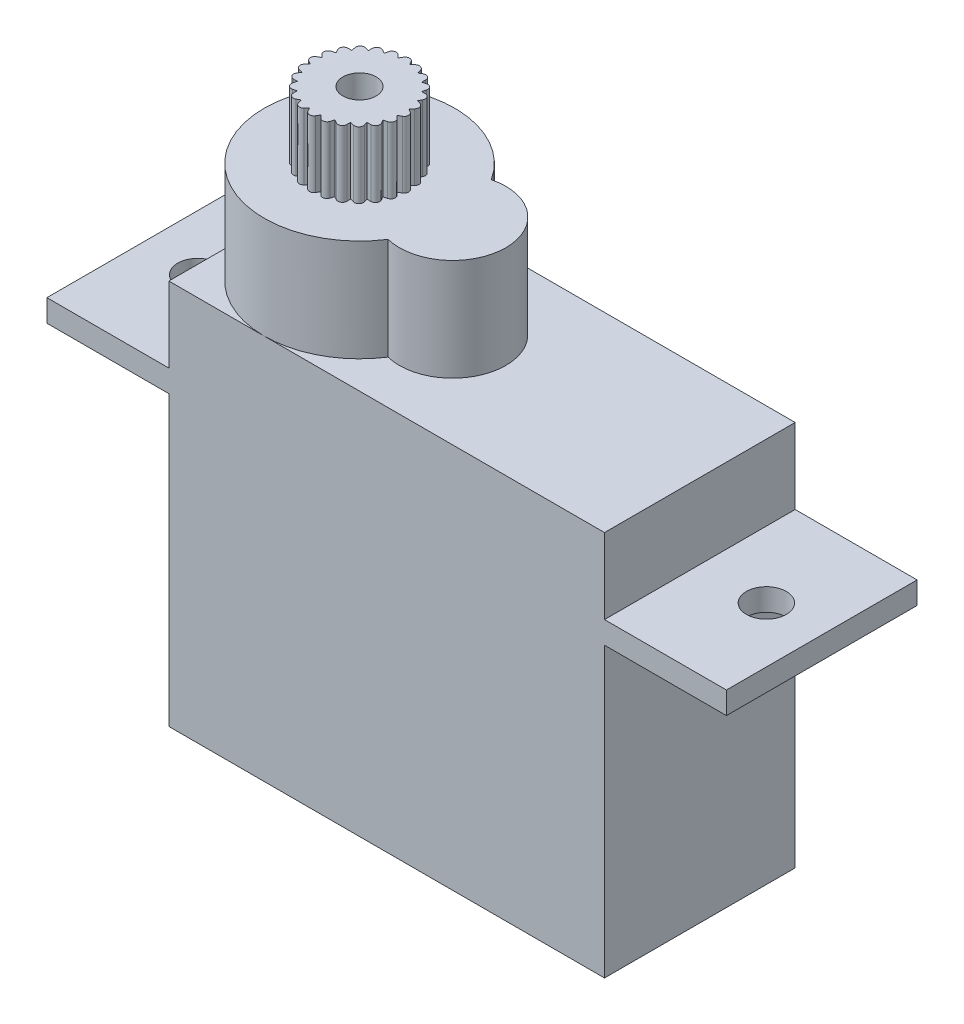
SolidWorks part; units mm, degrees
ref_plane "Plano frontal" through (0, 0, 0) normal (0, 0, 1) x (1, 0, 0)
ref_plane "Plano superior" through (0, 0, 0) normal (0, 1, 0) x (1, 0, 0)
ref_plane "Plano direito" through (0, 0, 0) normal (1, 0, 0) x (0, 0, -1)
sketch "Esboço1" plane through (0, 0, 0) normal (0, 0, 1) x (1, 0, 0)
  line L0 (0, 0) -> (0, 13)
  line L1 (0, 13) -> (-5.5, 13)
  line L2 (-5.5, 13) -> (-5.5, 14)
  line L3 (-5.5, 14) -> (0, 14)
  line L4 (0, 14) -> (0, 17.4)
  line L5 (0, 17.4) -> (19.65, 17.4)
  line L6 (19.65, 17.4) -> (19.65, 14)
  line L7 (19.65, 14) -> (25.15, 14)
  line L8 (25.15, 14) -> (25.15, 13)
  line L9 (25.15, 13) -> (19.65, 13)
  line L10 (19.65, 13) -> (19.65, 0)
  line L11 (19.65, 0) -> (0, 0)
  dimension "D1" = 19.65
  dimension "D2" = 17.4
  dimension "D3" = 30.65
  dimension "D4" = 1
  dimension "D5" = 5.5
  dimension "D7" = 13
  dimension "D6" = 5.5
extrude "Ressalto-extrusão1" add sketch "Esboço1" along normal blind 8.6
sketch "Esboço2" plane through (0, 14, 0) normal (0, 1, 0) x (1, 0, 0)
  line L0 (0, 0) -> (-5.5, 0) construction
  line L1 (-5.5, -8.6) -> (-5.5, 0) construction
  line L2 (25.15, -8.6) -> (25.15, 0) construction
  circle A0 centre (-3, -4.3) radius 0.9
  circle A1 centre (22.65, -4.3) radius 0.9
  dimension "D1" = 1.8
  dimension "D2" = 4.3
  dimension "D3" = 2.5
  dimension "D4" = 2.5
extrude "Corte-extrusão1" cut sketch "Esboço2" against normal through all
sketch "Esboço3" plane through (0, 17.4, 0) normal (0, 1, 0) x (1, 0, 0)
  line L0 (0, -8.6) -> (0, 0) construction
  line L4 (-5.5, -4.3) -> (25.15, -4.3) construction
  line L5 (8.5, -6.7) -> (8.7336, -6.7)
  line L6 (8.5, -6.7) -> (6.1, -6.7)
  line L7 (8.5, -1.9) -> (6.1, -1.9)
  line L8 (6.1, -1.9) -> (6.1, -6.7)
  line L9 (-5.5, -8.6) -> (-5.5, 0) construction
  line L10 (25.15, -8.6) -> (25.15, 0) construction
  circle A0 centre (4.3, -4.3) radius 4.3
  circle A1 centre (8.5, -4.3) radius 2.4
  dimension "D2" = 4.8
  dimension "D1" = 8.6
  dimension "D3" = 8.5
extrude "Ressalto-extrusão3" add sketch "Esboço3" along normal blind 4.6 contours A0 L4 L8 L7 | L4 A0 L6 L8 | A1 A0 L7 L8 | A1 L4 A0 | A0 L4 A1 | L4 A0 A1 | L4 A1 A0 | A1 L8 L6 A0
sketch "Esboço4" plane through (0, 22, 0) normal (0, 1, 0) x (1, 0, 0)
  circle A0 centre (4.3, -4.3) radius 1.9
  arc A1 (7.9155, -1.9723) -> (7.9155, -6.6277) centre (4.3, -4.3) ccw construction
  circle A2 centre (4.3, -4.3) radius 0.75
  dimension "D1" = 3.8
  dimension "D2" = 1.5
extrude "Ressalto-extrusão4" add sketch "Esboço4" along normal blind 3
sketch "Esboço5" plane through (0, 25, 0) normal (0, 1, 0) x (1, 0, 0)
  line L0 (3.9961, -2.4245) -> (4.1471, -2.1647)
  line L1 (4.4935, -2.1657) -> (4.6461, -2.4318)
  line L2 (3.9961, -2.4245) -> (4.6461, -2.4318)
  circle A0 centre (4.3, -4.3) radius 1.9 construction
  circle A1 centre (4.3, -4.3) radius 1.9 construction
  arc A2 (4.1471, -2.1647) -> (4.4935, -2.1657) centre (4.32, -2.2652) cw
  point P6 (4.3211, -2.4281)
  point P10 (4.3211, -1.8652)
  dimension "D3" = 0.2
  dimension "D1" = 0.65
  dimension "D2" = 60
extrude "Ressalto-extrusão5" add sketch "Esboço5" against normal blind 3
pattern_circular "PadrãoCircular1" count 24 over 360 about axis through (4.3, 0, 4.3) along (0, 1, 0) of "Ressalto-extrusão5"
equation "\"D3@Esboço1\"=\"D1@Esboço1\"+\"D5@Esboço1\"+\"D5@Esboço1\""
equation "\"D3@Esboço3\"=10.9-(\"D2@Esboço3\"/2)"
